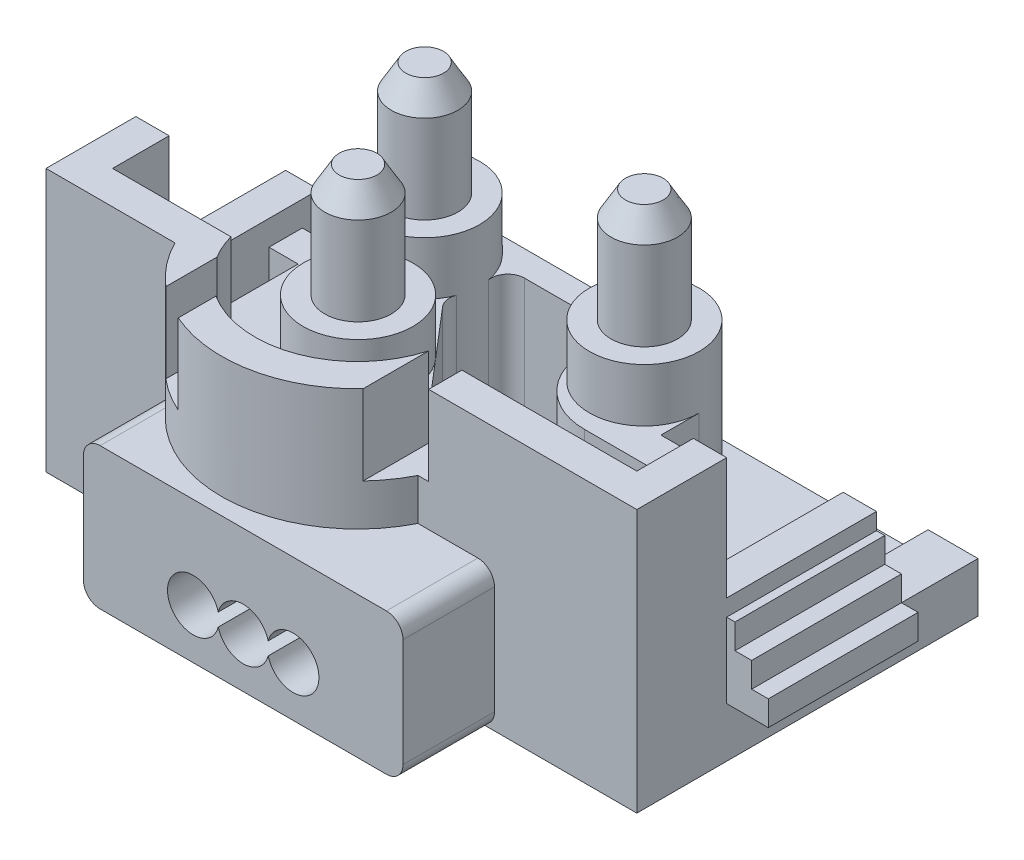
SolidWorks part; units mm, degrees
ref_plane "Front Plane" through (0, 0, 0) normal (0, 0, 1) x (1, 0, 0)
ref_plane "Top Plane" through (0, 0, 0) normal (0, 1, 0) x (1, 0, 0)
ref_plane "Right Plane" through (0, 0, 0) normal (1, 0, 0) x (0, 0, -1)
sketch "Sketch1" plane through (0, 0, 0) normal (0, 1, 0) x (1, 0, 0)
  line L1 (-17.75, 10.25) -> (17.75, 10.25)
  line L2 (-17.75, 10.25) -> (-17.75, -10.25)
  line L3 (-17.75, -10.25) -> (17.75, -10.25)
  line L4 (17.75, 10.25) -> (17.75, -10.25)
  dimension "D1" = 35.5
  dimension "D2" = 20.5
  dimension "D3" = 10.25
  dimension "D4" = 17.75
extrude "Boss-Extrude1" add sketch "Sketch1" along normal blind 1.5
sketch "Sketch2" plane through (0, 1.5, 0) normal (0, 1, 0) x (1, 0, 0)
  line L0 (17.75, 10.25) -> (14.75, 10.25)
  line L1 (17.75, 10.25) -> (-17.75, 10.25) construction
  line L2 (14.75, 10.25) -> (14.75, -8.25)
  line L3 (14.75, -8.25) -> (-14.75, -8.25)
  line L4 (-14.75, -8.25) -> (-14.75, 10.25)
  line L5 (-14.75, 10.25) -> (-17.75, 10.25)
  line L6 (-17.75, 10.25) -> (-17.75, -10.25)
  line L7 (-17.75, -10.25) -> (17.75, -10.25)
  line L8 (17.75, -10.25) -> (17.75, 10.25)
  dimension "D1" = 3
  dimension "D2" = 3
  dimension "D3" = 2
extrude "Boss-Extrude2" add sketch "Sketch2" along normal blind 1.5
sketch "Sketch4" plane through (0, 1.5, 0) normal (0, 1, 0) x (1, 0, 0)
  line L0 (6.5, 4.75) -> (-6.7, 4.75)
  line L1 (-10, 1.45) -> (-10, -0.85)
  line L2 (9.0993, -1.85) -> (-11.6277, -1.85) construction
  line L3 (9.8, 1.45) -> (9.8, -0.85)
  line L4 (14.75, -8.25) -> (-14.75, -8.25) construction
  line L5 (14.75, -8.25) -> (-14.75, -8.25) construction
  line L6 (-10, -0.85) -> (-11.75, -0.85)
  line L7 (-11.75, -0.85) -> (-11.75, -2.85)
  line L8 (-11.75, -2.85) -> (-10, -2.85)
  line L9 (9.8, -0.85) -> (11.55, -0.85)
  line L10 (11.55, -0.85) -> (11.55, -2.85)
  line L11 (11.55, -2.85) -> (9.8, -2.85)
  line L12 (-10, -2.85) -> (-10, -8.25)
  line L13 (9.8, -2.85) -> (7.2, -2.85)
  line L14 (3.2, 1.45) -> (3.2, 1.15)
  line L15 (3, -8.25) -> (-3.4405, -0.7293)
  line L16 (-17.75, -10.25) -> (17.75, -10.25) construction
  line L17 (-2.4691, 3.2179) -> (2.2691, 3.2179)
  line L18 (-14.75, -8.25) -> (-14.75, 10.25) construction
  line L19 (-3.4, 1.45) -> (-3.4, -5.85) construction
  line L21 (-3.4, -5.85) -> (-11.3408, -5.85) construction
  line L22 (-10, -10.25) -> (-10, -8.25)
  line L23 (4.6, -10.25) -> (4.6, -8.25)
  line L24 (4.6, -8.25) -> (3, -8.25)
  arc A0 (-10, 1.45) -> (-6.7, 4.75) centre (-6.7, 1.45) cw
  arc A1 (9.8, 1.45) -> (6.5, 4.75) centre (6.5, 1.45) ccw
  arc A2 (3.253, 2.0393) -> (3.2, 1.45) centre (6.5, 1.45) ccw
  arc A3 (7.2, -2.85) -> (3.2, 1.15) centre (7.2, 1.15) cw
  arc A4 (3.253, 2.0393) -> (2.2691, 3.2179) centre (2.2691, 2.2179) ccw
  arc A5 (-6.7, 4.75) -> (-10, 1.45) centre (-6.7, 1.45) ccw
  arc A6 (-3.453, 2.0393) -> (-2.4691, 3.2179) centre (-2.4691, 2.2179) cw
  arc A7 (9.8, 1.45) -> (6.5, 4.75) centre (6.5, 1.45) ccw
  arc A8 (-6.7, 4.75) -> (-10, 1.45) centre (-6.7, 1.45) ccw
  circle A9 centre (-3.4, -5.85) radius 3.3 construction
  arc A10 (-3.6156, 0.2767) -> (-3.453, 2.0393) centre (-6.7, 1.45) ccw
  arc A11 (-3.6156, 0.2767) -> (-3.4405, -0.7293) centre (-2.681, -0.0789) ccw
  arc A14 (4.6, -10.25) -> (-10, -10.25) centre (-2.7, -6.5789) cw
  point P31 (-3.8631, -0.2358)
  point P35 (-3.9135, 3.2179)
  point P36 (9.8, 0.3)
  line M2 (-14.75, -8.25) -> (14.75, -8.25)
  dimension "D1" = 3.3
  dimension "D2" = 3.3
  dimension "D8" = 4
  dimension "D9" = 1
  dimension "D10" = 1
  dimension "D11" = 19.8
  dimension "D16" = 10.6
  dimension "D17" = 6.6
  dimension "D18" = 1
  dimension "D19" = 4.5
  dimension "D3" = 3.3
  dimension "D4" = 2
  dimension "D5" = 1
  dimension "D6" = 2
  dimension "D7" = 13
  dimension "D12" = 1.75
  dimension "D13" = 1.75
  dimension "D14" = 3
  dimension "D15" = 13
  dimension "D20" = 14.6
extrude "Boss-Extrude4" add sketch "Sketch4" along normal blind 9.5 contours A11 A10 A6 L17 A4 A2 L14 A3 L13 L11 L10 L9 L3 A1 L0 A0 L1 L6 L7 L8 L12 L15 M2 | A14 L23 L22 M2
sketch "Sketch6" plane through (0, 11, 0) normal (0, 1, 0) x (1, 0, 0)
  line L0 (-6.7, 4.75) -> (-6.7, 1.45) construction
  line L1 (-10, 1.45) -> (-6.7, 1.45) construction
  line L2 (-3.4, 1.45) -> (-3.4, -5.85) construction
  line L3 (-11.3268, -5.85) -> (-3.4, -5.85) construction
  line L4 (6.5, 4.75) -> (-6.7, 4.75) construction
  circle A0 centre (-6.7, 1.45) radius 3.3
  circle A1 centre (6.5, 1.45) radius 3.3
  circle A2 centre (-3.4, -5.85) radius 3.3
  dimension "D1" = 10.6
extrude "Boss-Extrude5" add sketch "Sketch6" along normal blind 3.2
sketch "Sketch7" plane through (0, 14.2, 0) normal (0, 1, 0) x (1, 0, 0)
  circle A1 centre (-6.7, 1.45) radius 2
  circle A2 centre (-3.4, -5.85) radius 2
  circle A3 centre (6.5, 1.45) radius 2
  dimension "D1" = 4
  dimension "D2" = 4
  dimension "D3" = 4
extrude "Boss-Extrude6" add sketch "Sketch7" along normal blind 6.8 separate body
chamfer "Chamfer1" distance 1.5 angle 30 1 edges at (-3.4, 21, 7.85)
chamfer "Chamfer2" distance 1.5 angle 30 1 edges at (6.5, 21, 0.55)
chamfer "Chamfer3" distance 1.5 angle 30 1 edges at (-6.7, 21, 0.55)
sketch "Sketch8" plane through (0, 3, 0) normal (0, 1, 0) x (1, 0, 0)
  line L0 (-17.75, -10.25) -> (-10, -10.25) construction
  line L1 (-10, -8.25) -> (-14.75, -8.25) construction
  line L2 (14.75, -8.25) -> (4.6, -8.25) construction
  line L3 (4.6, -10.25) -> (17.75, -10.25) construction
  line L4 (-17.75, -10.25) -> (-10, -10.25)
  line L5 (-10, -8.25) -> (-14.75, -8.25)
  line L6 (14.75, -8.25) -> (4.6, -8.25)
  line L7 (4.6, -10.25) -> (17.75, -10.25)
  line L8 (17.75, -10.25) -> (17.75, -4.85)
  line L9 (17.75, -10.25) -> (17.75, 10.25) construction
  line L12 (15.75, -4.85) -> (17.75, -4.85)
  line L13 (-17.75, -10.25) -> (-17.75, -4.85)
  line L14 (-17.75, 10.25) -> (-17.75, -10.25) construction
  line L15 (-17.75, -4.85) -> (-15.75, -4.85)
  line L18 (4.6, -8.25) -> (3.2405, -8.25)
  line L19 (-10, -8.25) -> (-8.6405, -8.25)
  line L20 (14.75, -8.25) -> (15.75, -8.25)
  line L21 (15.75, -8.25) -> (15.75, -4.85)
  line L22 (-14.75, -8.25) -> (-15.75, -8.25)
  line L23 (-15.75, -8.25) -> (-15.75, -4.85)
  arc A0 (-10, -10.25) -> (4.6, -10.25) centre (-2.7, -6.5789) ccw construction
  arc A1 (-10, -10.25) -> (4.6, -10.25) centre (-2.7, -6.5789) ccw
  arc A3 (-8.6405, -8.25) -> (3.2405, -8.25) centre (-2.7, -6.5789) ccw
  dimension "D4" = 2
  dimension "D1" = 5.4
  dimension "D2" = 5.4
  dimension "D3" = 2
extrude "Boss-Extrude7" add sketch "Sketch8" along normal up to surface (8 mm away) up to face at (7.9245, 11, 1.0683)
sketch "Sketch9" plane through (0, 11, 0) normal (0, 1, 0) x (1, 0, 0)
  line L12 (-17.75, -4.85) -> (-17.75, -10.25) construction
  line L13 (-17.75, -10.25) -> (-10, -10.25) construction
  line L14 (4.6, -10.25) -> (17.75, -10.25) construction
  line L15 (17.75, -10.25) -> (17.75, -4.85) construction
  line L17 (17.75, -10.25) -> (17.75, -4.85)
  line L21 (-17.75, -4.85) -> (-17.75, -10.25)
  line L22 (-17.75, -10.25) -> (-10, -10.25)
  line L23 (5.2405, -10.25) -> (17.75, -10.25)
  line L27 (3, -8.25) -> (15.75, -8.25) construction
  line L28 (3.2405, -8.25) -> (3.2405, -12.1893)
  line L29 (5.2405, -8.25) -> (5.2405, -10.25)
  line L30 (-8, -12.798) -> (-8, -9.74)
  line L31 (-6, -11.7935) -> (-6, -14.054)
  line L32 (17.75, -4.85) -> (15.75, -4.85)
  line L36 (15.75, -4.85) -> (15.75, -8.25)
  line L37 (15.75, -4.85) -> (15.75, -8.25) construction
  line L38 (15.75, -4.85) -> (15.75, -8.25) construction
  line L39 (15.75, -8.25) -> (5.2405, -8.25)
  line L40 (-17.75, -4.85) -> (-15.75, -4.85)
  line L41 (-15.75, -4.85) -> (-15.75, -8.25)
  line L42 (-15.75, -8.25) -> (-8.6405, -8.25)
  arc A4 (-10, -10.25) -> (4.6, -10.25) centre (-2.7, -6.5789) ccw construction
  arc A5 (-10, -10.25) -> (-8, -12.798) centre (-2.7, -6.5789) ccw
  arc A6 (-6, -14.054) -> (3.2405, -12.1893) centre (-2.7, -6.5789) ccw
  arc A7 (-8.6405, -8.25) -> (-8, -9.74) centre (-2.7, -6.5789) ccw
  arc A8 (-6, -11.7935) -> (3.2405, -8.25) centre (-2.7, -6.5789) ccw
  dimension "D2" = 2
  dimension "D1" = 2
  dimension "D3" = 2
extrude "Boss-Extrude8" add sketch "Sketch9" along normal blind 4.8
sketch "Sketch10" plane through (0, 0, 10.25) normal (0, 0, 1) x (1, 0, 0)
  line L0 (-10, 1) -> (-10, 7.5)
  line L1 (-17.75, 0) -> (17.75, 0) construction
  line L2 (-9, 8.5) -> (8.2, 8.5)
  line L3 (9.2, 7.5) -> (9.2, 1)
  line L4 (8.2, 0) -> (-9, 0)
  line L5 (-10, 15.8) -> (-10, 1.5) construction
  arc A0 (9.2, 7.5) -> (8.2, 8.5) centre (8.2, 7.5) ccw
  arc A1 (9.2, 1) -> (8.2, 0) centre (8.2, 1) cw
  arc A2 (-9, 0) -> (-10, 1) centre (-9, 1) cw
  arc A3 (-10, 7.5) -> (-9, 8.5) centre (-9, 7.5) cw
  point P12 (9.2, 0)
  point P15 (-10, 0)
  dimension "D4" = 1
  dimension "D1" = 19.2
  dimension "D2" = 8.5
  dimension "D3" = 0
extrude "Boss-Extrude9" add sketch "Sketch10" along normal blind 5.5
sketch "Sketch11" plane through (0, 0, 4.85) normal (0, 0, -1) x (-1, 0, 0)
  line L2 (-15.75, 8.5) -> (-17.75, 8.5)
  line L3 (-17.75, 15.8) -> (-17.75, 3) construction
  line L4 (-17.75, 8.5) -> (-17.75, 7.5)
  line L5 (-17.75, 7.5) -> (-18.25, 7.5)
  line L6 (-18.25, 7.5) -> (-18.25, 6)
  line L7 (-18.25, 6) -> (-19.25, 6)
  line L8 (-19.25, 6) -> (-19.25, 4.5)
  line L9 (-19.25, 4.5) -> (-20.25, 4.5)
  line L10 (-20.25, 4.5) -> (-20.25, 3)
  line L11 (-20.25, 3) -> (-15.75, 3)
  line L12 (0, 0) -> (0, 19.6227) construction
  line L13 (-15.75, 8.5) -> (-15.75, 3)
  line L14 (-15.75, 15.8) -> (-15.75, 3) construction
  line L15 (20.25, 4.5) -> (20.25, 3)
  line L16 (19.25, 4.5) -> (20.25, 4.5)
  line L17 (19.25, 6) -> (19.25, 4.5)
  line L18 (18.25, 6) -> (19.25, 6)
  line L19 (18.25, 7.5) -> (18.25, 6)
  line L20 (17.75, 7.5) -> (18.25, 7.5)
  line L21 (17.75, 8.5) -> (17.75, 7.5)
  line L22 (15.75, 8.5) -> (17.75, 8.5)
  line L23 (15.75, 8.5) -> (15.75, 3)
  line L24 (20.25, 3) -> (15.75, 3)
  dimension "D1" = 5.5
  dimension "D2" = 1.5
  dimension "D3" = 1.5
  dimension "D4" = 1.5
  dimension "D5" = 4.5
  dimension "D6" = 3.5
  dimension "D7" = 2.5
extrude "Boss-Extrude10" add sketch "Sketch11" along normal blind 9
sketch "Sketch12" plane through (0, 0, 8.25) normal (0, 0, -1) x (-1, 0, 0)
  line L0 (-8.75, 1.5) -> (-8.75, 6.6)
  line L1 (-14.75, 1.5) -> (-3, 1.5) construction
  line L2 (-6.35, 9) -> (-6.15, 9)
  line L3 (-3.75, 6.6) -> (-3.75, 1.5)
  line L4 (-3, 1.5) -> (3.4405, 1.5) construction
  line L5 (-3.75, 1.5) -> (-8.75, 1.5)
  line L6 (-15.75, 15.8) -> (-15.75, 3) construction
  arc A0 (-3.75, 6.6) -> (-6.15, 9) centre (-6.15, 6.6) ccw
  arc A1 (-8.75, 6.6) -> (-6.35, 9) centre (-6.35, 6.6) cw
  dimension "D3" = 2.4
  dimension "D1" = 7.5
  dimension "D2" = 5
  dimension "D4" = 7
extrude "Boss-Extrude11" add sketch "Sketch12" along normal blind 9
sketch "Sketch13" plane through (0, 0, 15.75) normal (0, 0, 1) x (1, 0, 0)
  line L0 (-10, 3) -> (-3.4, 3) construction
  line L1 (-0.4, 3) -> (-1.95, 3) construction
  line L2 (-10, 7.5) -> (-10, 1) construction
  line L3 (9.2, 1) -> (9.2, 7.5) construction
  line L4 (-9, 0) -> (8.2, 0) construction
  line L5 (-0.4, 3) -> (-0.4, 6.3365) construction
  line L6 (-0.4, 3) -> (1.15, 3) construction
  line L7 (-1.95, 3) -> (1.15, 3) construction
  line L8 (4.15, 3) -> (9.2, 3) construction
  arc A0 (-1.9, 2.6095) -> (1.1, 2.6095) centre (-0.4, 3) ccw
  arc A1 (-1.9, 3.3905) -> (-1.9, 2.6095) centre (-3.4, 3) ccw
  arc A2 (1.1, 2.6095) -> (1.1, 3.3905) centre (2.6, 3) ccw
  arc A3 (1.1, 3.3905) -> (-1.9, 3.3905) centre (-0.4, 3) ccw
  dimension "D2" = 3.1
  dimension "D6" = 3.1
  dimension "D7" = 3.1
  dimension "D1" = 3
  dimension "D3" = 0
  dimension "D4" = 3
  dimension "D5" = 3
extrude "Cut-Extrude4" cut sketch "Sketch13" against normal up to surface (5.5 mm away) up to face at (-12.4512, 6.6488, 10.25)
